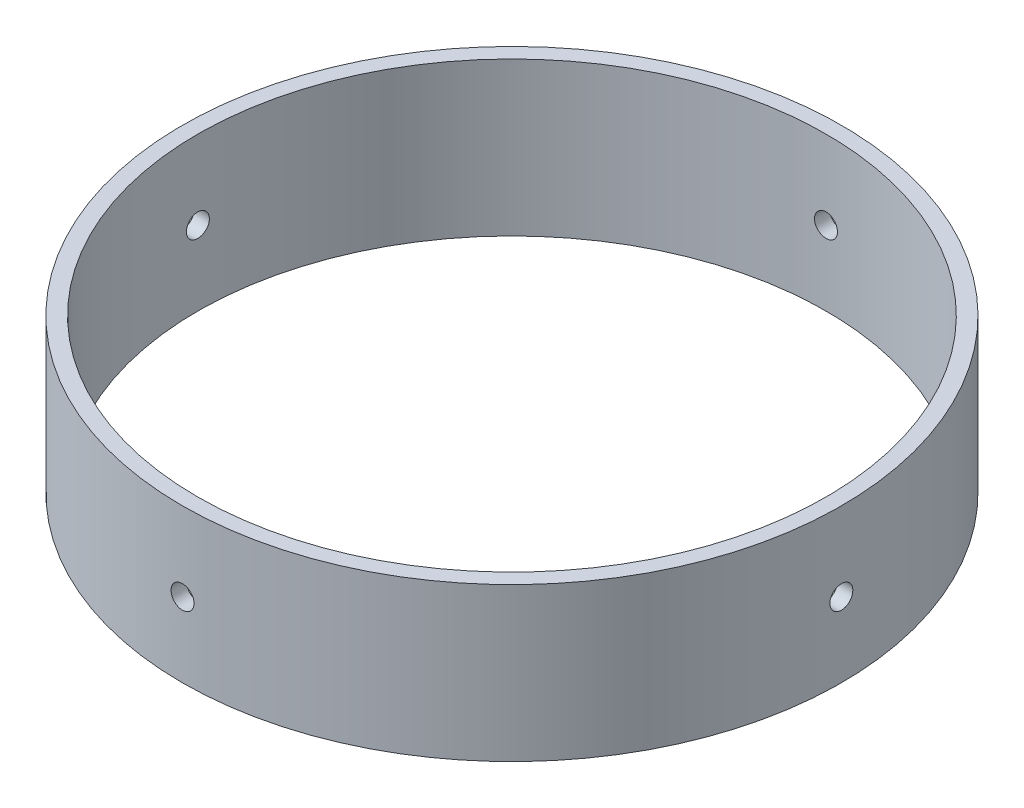
SolidWorks part; units mm, degrees
ref_plane "Front Plane" through (0, 0, 0) normal (0, 0, 1) x (1, 0, 0)
ref_plane "Top Plane" through (0, 0, 0) normal (0, 1, 0) x (1, 0, 0)
ref_plane "Right Plane" through (0, 0, 0) normal (1, 0, 0) x (0, 0, -1)
sketch "Sketch1" plane through (0, 0, 0) normal (0, 1, 0) x (1, 0, 0)
  circle A0 centre (0, 0) radius 52.07
  circle A1 centre (0, 0) radius 54.61
  dimension "D1" = 104.14
  dimension "D2" = 2.54
extrude "Boss-Extrude1" add sketch "Sketch1" along normal blind 25.4
sketch "Sketch3" plane through (0, 0, 0) normal (0, 0, 1) x (1, 0, 0)
  circle A0 centre (0, 12.329) radius 1.905
  dimension "D1" = 3.81
extrude "Cut-Extrude1" cut sketch "Sketch3" along normal through all
pattern_circular "CirPattern1" count 4 over 360 about axis through (0, 25.4, 0) along (0, 1, 0) of "Cut-Extrude1"
